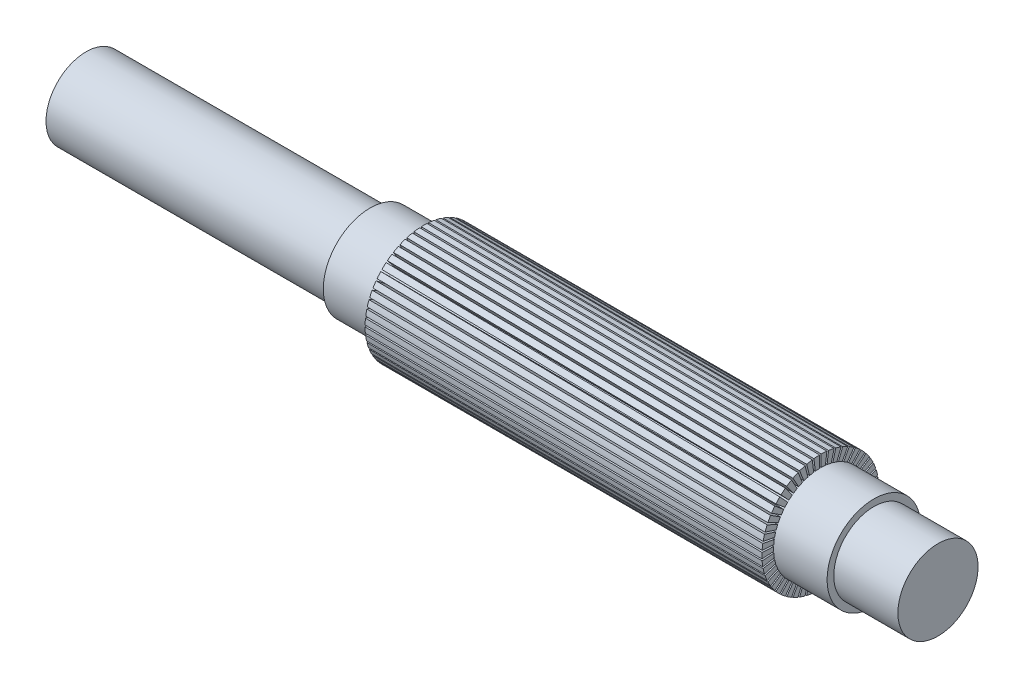
SolidWorks part; units mm, degrees
ref_plane "Front Plane" through (0, 0, 0) normal (0, 0, 1) x (1, 0, 0)
ref_plane "Top Plane" through (0, 0, 0) normal (0, 1, 0) x (1, 0, 0)
ref_plane "Right Plane" through (0, 0, 0) normal (1, 0, 0) x (0, 0, -1)
sketch "Sketch2" plane through (0, 0, 0) normal (0, 0, 1) x (1, 0, 0)
  line L0 (-127.5, 0) -> (127.5, 0) construction
  line L1 (-127.5, 0) -> (-127.5, 12)
  line L2 (-127.5, 12) -> (-42.5, 12)
  line L3 (-42.5, 12) -> (-42.5, 14)
  line L4 (-42.5, 14) -> (-26.5, 14)
  line L5 (92.3, 14) -> (108.3, 14)
  line L7 (-26.5, 14) -> (-26.5, 17.5)
  line L8 (-26.5, 17.5) -> (92.3, 17.5)
  line L9 (92.3, 17.5) -> (92.3, 14)
  line L13 (108.3, 14) -> (108.3, 12)
  line L14 (108.3, 12) -> (127.5, 12)
  line L15 (127.5, 12) -> (127.5, 0)
  line L16 (127.5, 0) -> (-127.5, 0)
  point P4 (0, 0)
  dimension "D1" = 255
  dimension "D2" = 118.8
  dimension "D3" = 85
  dimension "D4" = 16
  dimension "D5" = 16
  dimension "D6" = 35
  dimension "D7" = 24
  dimension "D8" = 2
revolve "Revolve3" add sketch "Sketch2" angle 360 about L0
sketch "Sketch3" plane through (92.3, 0, 0) normal (1, 0, 0) x (0, 0, -1)
  line L0 (-0.25, 17.9978) -> (-0.25, 13.9978)
  line L1 (0.25, 17.9978) -> (0.25, 13.9978)
  line L2 (-0.25, 15.9978) -> (0.25, 15.9978) construction
  line L3 (-0.25, 17.9978) -> (0.25, 17.9978)
  circle A0 centre (0, 0) radius 14 construction
  arc A2 (0.25, 13.9978) -> (-0.25, 13.9978) centre (0, 0) ccw
  point P12 (0, 15.9978)
  dimension "D1" = 0.5
  dimension "D2" = 4
sketch "Sketch4" plane through (-26.5, 0, 0) normal (-1, 0, 0) x (0, 0, 1)
  line L0 (-1.5252, 17.4334) -> (0, 0) construction
  line L1 (0, 0) -> (0, 22.2505) construction
  line L2 (-1.2202, 13.9467) -> (-1.5252, 17.4334)
  line L3 (-1.0265, 17.4699) -> (-0.7213, 13.9814)
  circle A0 centre (0, 0) radius 14 construction
  circle A1 centre (0, 0) radius 17.5
  arc A2 (-1.0265, 17.4699) -> (-1.5252, 17.4334) centre (0, 0) ccw
  circle A3 centre (0, 0) radius 14 construction
  arc A4 (-0.7213, 13.9814) -> (-1.2202, 13.9467) centre (0, 0) ccw
  point P13 (-1.2202, 13.9467)
  dimension "D2" = 5
  dimension "D3" = 0.5
  dimension "D1" = 0
loft "Cut-Loft1" cut profiles "Sketch3", "Sketch4"
pattern_circular "CirPattern1" count 50 over 360 about axis through (-127.5, 0, 0) along (-1, 0, 0) of "Cut-Loft1"
